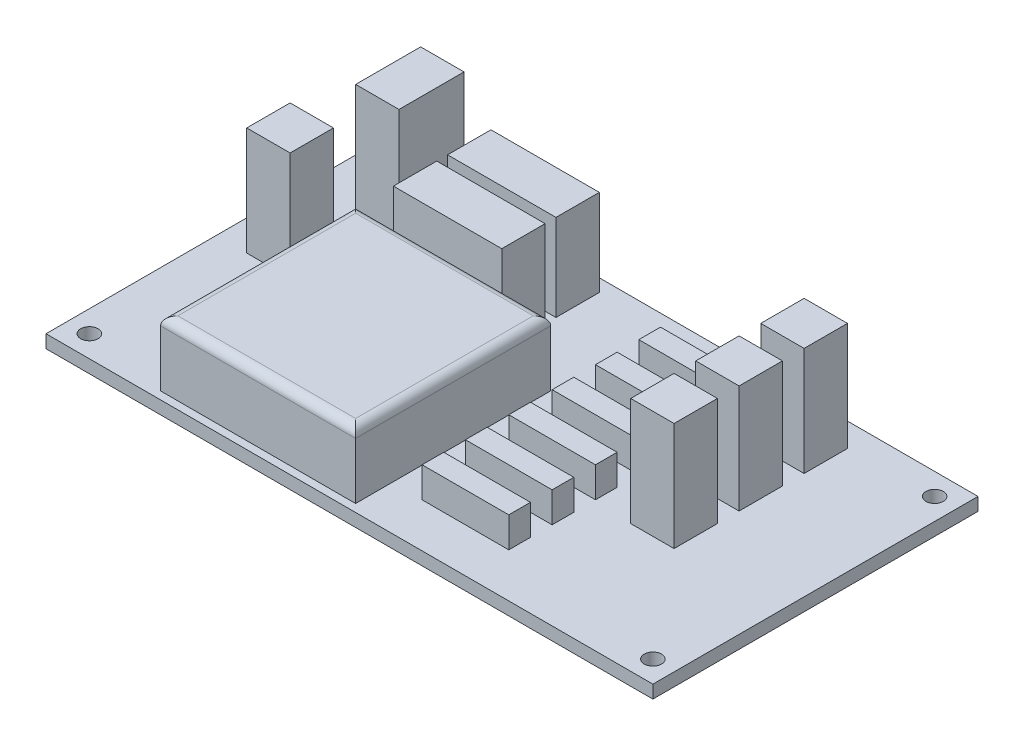
SolidWorks part; units mm, degrees
ref_plane "Face" through (0, 0, 0) normal (0, 0, 1) x (1, 0, 0)
ref_plane "Dessus" through (0, 0, 0) normal (0, 1, 0) x (1, 0, 0)
ref_plane "Droite" through (0, 0, 0) normal (1, 0, 0) x (0, 0, -1)
sketch "Esquisse1" plane through (0, 0, 0) normal (0, 1, 0) x (1, 0, 0)
  line L0 (70, 75) -> (70, 0) construction
  line L1 (0, 0) -> (140, 0)
  line L2 (0, 0) -> (0, 75)
  line L3 (0, 75) -> (140, 75)
  line L4 (140, 0) -> (140, 75)
  line L5 (0, 37.5) -> (140, 37.5) construction
  circle A0 centre (5, 70) radius 2
  circle A1 centre (135, 70) radius 2
  circle A2 centre (135, 5) radius 2
  circle A3 centre (5, 5) radius 2
  dimension "D3" = 4
  dimension "D1" = 140
  dimension "D2" = 75
  dimension "D4" = 5
  dimension "D5" = 5
extrude "Extrusion1" add sketch "Esquisse1" along normal blind 3
sketch "Esquisse2" plane through (0, 3, 0) normal (0, 1, 0) x (1, 0, 0)
  line L1 (24.6298, 1.7887) -> (69.6298, 1.7887)
  line L2 (24.6298, 1.7887) -> (24.6298, 46.7887)
  line L3 (24.6298, 46.7887) -> (69.6298, 46.7887)
  line L4 (69.6298, 1.7887) -> (69.6298, 46.7887)
  dimension "D1" = 45
extrude "Extrusion2" add sketch "Esquisse2" along normal blind 15
fillet "Congé1" radius 2 4 edges at (47.1298, 18, -46.7887) (69.6298, 18, -24.2887) (47.1298, 18, -1.7887) (24.6298, 18, -24.2887)
sketch "Esquisse3" plane through (0, 3, 0) normal (0, 1, 0) x (1, 0, 0)
  line L0 (105.3706, 69.5153) -> (115.3706, 69.5153)
  line L1 (7.0385, 49.2711) -> (17.0385, 49.2711)
  line L2 (7.0385, 49.2711) -> (7.0385, 39.2711)
  line L3 (7.0385, 39.2711) -> (17.0385, 39.2711)
  line L4 (17.0385, 49.2711) -> (17.0385, 39.2711)
  line L13 (105.3706, 69.5153) -> (105.3706, 59.5153)
  line L14 (105.3706, 59.5153) -> (115.3706, 59.5153)
  line L15 (115.3706, 69.5153) -> (115.3706, 59.5153)
  line L16 (105.3706, 54.5153) -> (115.3706, 54.5153)
  line L17 (105.3706, 54.5153) -> (105.3706, 44.5153)
  line L18 (105.3706, 44.5153) -> (115.3706, 44.5153)
  line L19 (115.3706, 54.5153) -> (115.3706, 44.5153)
  line L20 (105.3706, 39.5153) -> (115.3706, 39.5153)
  line L21 (105.3706, 39.5153) -> (105.3706, 29.5153)
  line L22 (105.3706, 29.5153) -> (115.3706, 29.5153)
  line L23 (115.3706, 39.5153) -> (115.3706, 29.5153)
  line L25 (115.3706, 69.5153) -> (115.3706, 29.5153) construction
  dimension "D1" = 10
  dimension "D2" = 10
  dimension "D5" = 10
  dimension "D6" = 10
  dimension "D7" = 5
  dimension "D8" = 5
extrude "Extrusion3" add sketch "Esquisse3" along normal blind 25
sketch "Esquisse4" plane through (0, 3, 0) normal (0, 1, 0) x (1, 0, 0)
  line L1 (30.5777, 72.064) -> (55.5777, 72.064)
  line L2 (30.5777, 72.064) -> (30.5777, 62.064)
  line L3 (30.5777, 62.064) -> (55.5777, 62.064)
  line L4 (55.5777, 72.064) -> (55.5777, 62.064)
  line L5 (30.5777, 59.564) -> (55.5777, 59.564)
  line L6 (30.5777, 59.564) -> (30.5777, 49.564)
  line L7 (30.5777, 49.564) -> (55.5777, 49.564)
  line L8 (55.5777, 59.564) -> (55.5777, 49.564)
  dimension "D1" = 10
  dimension "D2" = 25
  dimension "D3" = 2.5
extrude "Extrusion4" add sketch "Esquisse4" along normal blind 20
sketch "Esquisse5" plane through (0, 3, 0) normal (0, 1, 0) x (1, 0, 0)
  line L0 (76.5574, 65.1975) -> (76.5574, 10.1975) construction
  line L1 (76.5574, 10.1975) -> (96.5574, 10.1975) construction
  line L2 (96.5574, 10.1975) -> (96.5574, 65.1975) construction
  line L3 (96.5574, 65.1975) -> (76.5574, 65.1975) construction
  line L5 (76.5574, 65.1975) -> (96.5574, 65.1975)
  line L6 (76.5574, 65.1975) -> (76.5574, 60.1975)
  line L7 (76.5574, 60.1975) -> (96.5574, 60.1975)
  line L8 (96.5574, 65.1975) -> (96.5574, 60.1975)
  line L9 (76.5574, 55.1975) -> (96.5574, 55.1975)
  line L10 (76.5574, 55.1975) -> (76.5574, 50.1975)
  line L11 (76.5574, 50.1975) -> (96.5574, 50.1975)
  line L12 (96.5574, 55.1975) -> (96.5574, 50.1975)
  line L13 (76.5574, 45.1975) -> (96.5574, 45.1975)
  line L14 (76.5574, 45.1975) -> (76.5574, 40.1975)
  line L15 (76.5574, 40.1975) -> (96.5574, 40.1975)
  line L16 (96.5574, 45.1975) -> (96.5574, 40.1975)
  line L17 (76.5574, 35.1975) -> (96.5574, 35.1975)
  line L18 (76.5574, 35.1975) -> (76.5574, 30.1975)
  line L19 (76.5574, 30.1975) -> (96.5574, 30.1975)
  line L20 (96.5574, 35.1975) -> (96.5574, 30.1975)
  line L21 (76.5574, 25.1975) -> (96.5574, 25.1975)
  line L22 (76.5574, 25.1975) -> (76.5574, 20.1975)
  line L23 (76.5574, 20.1975) -> (96.5574, 20.1975)
  line L24 (96.5574, 25.1975) -> (96.5574, 20.1975)
  line L25 (76.5574, 15.1975) -> (96.5574, 15.1975)
  line L26 (76.5574, 15.1975) -> (76.5574, 10.1975)
  line L27 (76.5574, 10.1975) -> (96.5574, 10.1975)
  line L28 (96.5574, 15.1975) -> (96.5574, 10.1975)
  dimension "D1" = 20
  dimension "D2" = 5
  dimension "D3" = 5
  dimension "D4" = 5
  dimension "D5" = 5
  dimension "D6" = 5
  dimension "D7" = 5
extrude "Extrusion5" add sketch "Esquisse5" along normal blind 7
sketch "Esquisse6" plane through (0, 3, 0) normal (0, 1, 0) x (1, 0, 0)
  line L1 (20.9042, 60.5245) -> (10.9042, 60.5245)
  line L2 (20.9042, 60.5245) -> (20.9042, 75.5245)
  line L3 (20.9042, 75.5245) -> (10.9042, 75.5245)
  line L4 (10.9042, 60.5245) -> (10.9042, 75.5245)
  dimension "D1" = 10
  dimension "D2" = 15
extrude "Extrusion6" add sketch "Esquisse6" along normal blind 25
